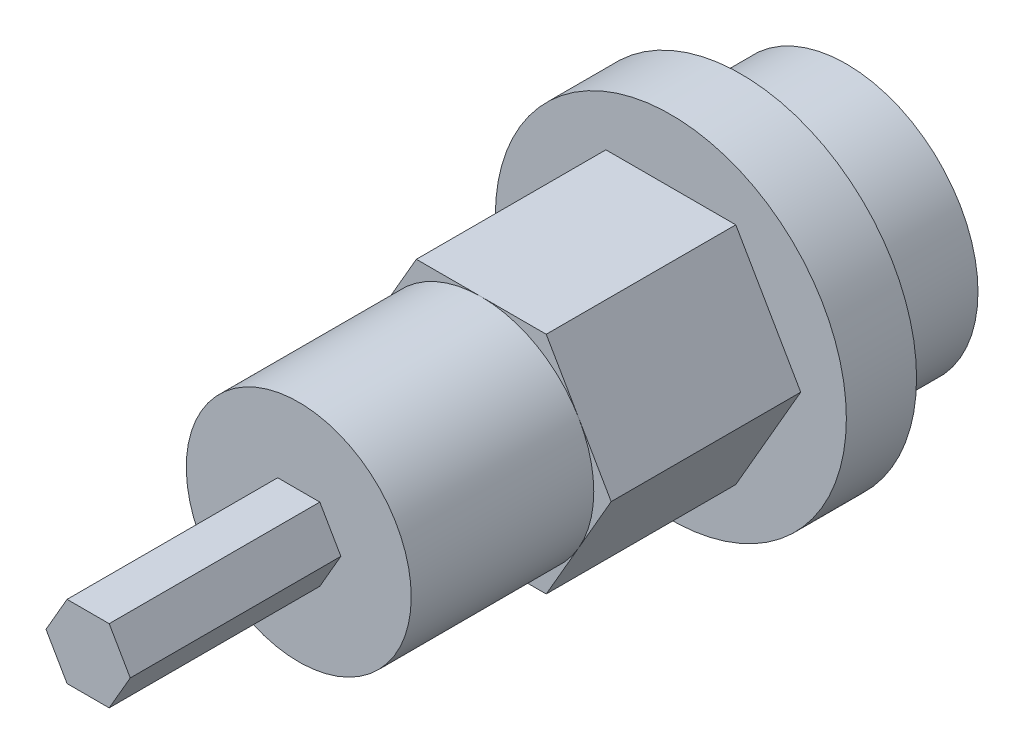
SolidWorks part; units mm, degrees
ref_plane "Front Plane" through (0, 0, 0) normal (0, 0, 1) x (1, 0, 0)
ref_plane "Top Plane" through (0, 0, 0) normal (0, 1, 0) x (1, 0, 0)
ref_plane "Right Plane" through (0, 0, 0) normal (1, 0, 0) x (0, 0, -1)
sketch "Sketch1" plane through (0, 0, 0) normal (0, 0, 1) x (1, 0, 0)
  circle A0 centre (0, 0) radius 3.75
  dimension "D1" = 7.5
extrude "Boss-Extrude1" add sketch "Sketch1" along normal blind 3
sketch "Sketch2" plane through (0, 0, 3) normal (0, 0, 1) x (1, 0, 0)
  circle A0 centre (0, 0) radius 5
  dimension "D1" = 10
extrude "Boss-Extrude2" add sketch "Sketch2" along normal blind 2
sketch "Sketch3" plane through (0, 0, 5) normal (0, 0, 1) x (1, 0, 0)
  line L7 (3.7, 0) -> (1.85, 3.2043)
  line L8 (1.85, 3.2043) -> (-1.85, 3.2043)
  line L9 (-1.85, 3.2043) -> (-3.7, 0)
  line L10 (-3.7, 0) -> (-1.85, -3.2043)
  line L11 (-1.85, -3.2043) -> (1.85, -3.2043)
  line L12 (1.85, -3.2043) -> (3.7, 0)
  circle A0 centre (0, 0) radius 3.7 construction
  circle A1 centre (0, 0) radius 3.2043 construction
  dimension "D1" = 7.4
extrude "Boss-Extrude3" add sketch "Sketch3" along normal blind 5.4
sketch "Sketch4" plane through (0, 0, 10.4) normal (0, 0, 1) x (1, 0, 0)
  line L2 (-1.85, 3.2043) -> (-3.7, 0) construction
  circle A0 centre (0, 0) radius 3.2043
extrude "Boss-Extrude4" add sketch "Sketch4" along normal blind 5.2
sketch "Sketch5" plane through (0, 0, 15.6) normal (0, 0, 1) x (1, 0, 0)
  line L1 (1.2, 0) -> (0.6, 1.0392)
  line L2 (0.6, 1.0392) -> (-0.6, 1.0392)
  line L3 (-0.6, 1.0392) -> (-1.2, 0)
  line L4 (-1.2, 0) -> (-0.6, -1.0392)
  line L5 (-0.6, -1.0392) -> (0.6, -1.0392)
  line L6 (0.6, -1.0392) -> (1.2, 0)
  circle A0 centre (0, 0) radius 1.0392 construction
  dimension "D1" = 1.2
extrude "Boss-Extrude5" add sketch "Sketch5" along normal blind 6
